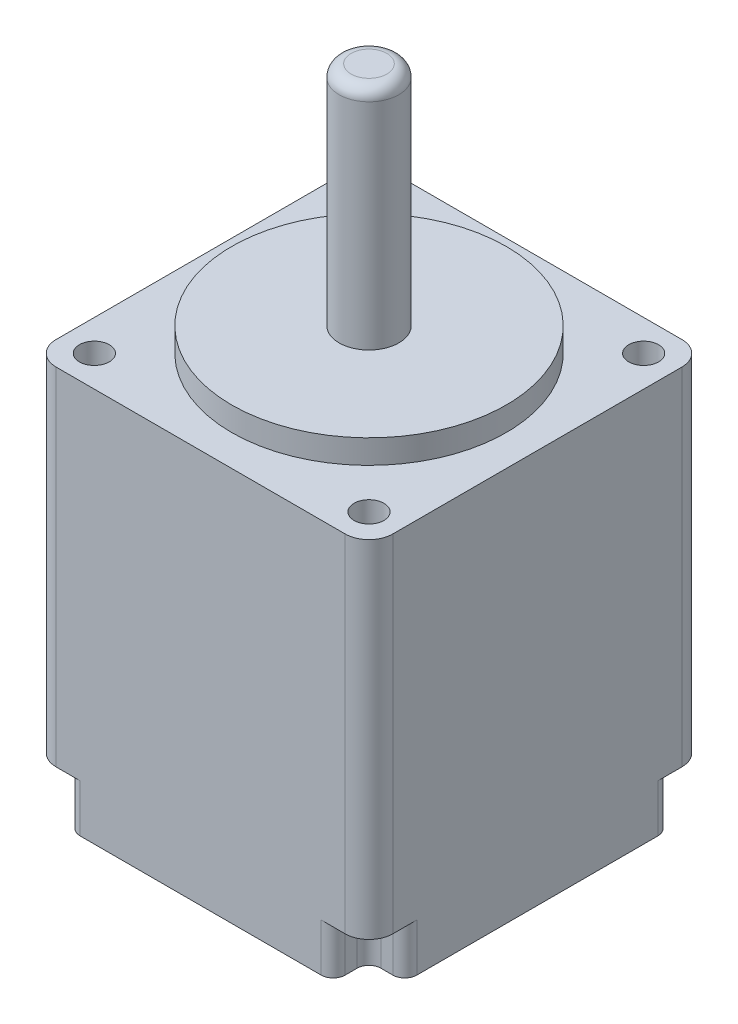
SolidWorks part; units mm, degrees
ref_plane "Front Plane" through (0, 0, 0) normal (0, 0, 1) x (1, 0, 0)
ref_plane "Top Plane" through (0, 0, 0) normal (0, 1, 0) x (1, 0, 0)
ref_plane "Right Plane" through (0, 0, 0) normal (1, 0, 0) x (0, 0, -1)
sketch "Sketch1" plane through (0, 0, 0) normal (0, 1, 0) x (1, 0, 0)
  line L1 (-14.1, 14.1) -> (14.1, 14.1)
  line L2 (-14.1, 14.1) -> (-14.1, -14.1)
  line L3 (-14.1, -14.1) -> (14.1, -14.1)
  line L4 (14.1, 14.1) -> (14.1, -14.1)
  line L5 (-14.1, 14.1) -> (14.1, -14.1) construction
  line L6 (-14.1, -14.1) -> (14.1, 14.1) construction
  point P0 (0, 0)
  dimension "D1" = 28.2
extrude "Boss-Extrude1" add sketch "Sketch1" along normal blind 33
sketch "Sketch2" plane through (0, 33, 0) normal (0, 1, 0) x (1, 0, 0)
  circle A0 centre (0, 0) radius 11.5
  dimension "D1" = 23
extrude "Boss-Extrude2" add sketch "Sketch2" along normal blind 2
sketch "Sketch3" plane through (0, 35, 0) normal (0, 1, 0) x (1, 0, 0)
  circle A0 centre (0, 0) radius 2.5
  dimension "D1" = 5
extrude "Boss-Extrude3" add sketch "Sketch3" along normal blind 19
sketch "Sketch4" plane through (0, 33, 0) normal (0, 1, 0) x (1, 0, 0)
  line L0 (14.1, 14.1) -> (-14.1, 14.1) construction
  line L1 (-14.1, 14.1) -> (-14.1, -14.1) construction
  circle A0 centre (-11.5, 11.5) radius 1.25
  dimension "D1" = 2.5
  dimension "D2" = 2.6
  dimension "D3" = 2.6
extrude "Cut-Extrude1" cut sketch "Sketch4" against normal blind 8
mirror "Mirror1" about plane through (0, 0, 0) normal (1, 0, 0) of "Cut-Extrude1"
mirror "Mirror2" about plane through (0, 0, 0) normal (0, 0, 1) of "Mirror1", "Cut-Extrude1"
sketch "Sketch5" plane through (0, 0, 0) normal (0, -1, 0) x (1, 0, 0)
  line L0 (-14.1, 14.1) -> (-11.1, 14.1)
  line L1 (-14.1, 14.1) -> (14.1, 14.1) construction
  line L2 (-11.1, 14.1) -> (-11.1, 11.1)
  line L3 (-11.1, 11.1) -> (-14.1, 11.1)
  line L5 (-14.1, 11.1) -> (-14.1, 14.1)
  dimension "D1" = 3
  dimension "D2" = 3
  dimension "D3" = 3
extrude "Cut-Extrude2" cut sketch "Sketch5" against normal blind 4
mirror "Mirror3" about plane through (0, 0, 0) normal (1, 0, 0) of "Cut-Extrude2"
mirror "Mirror4" about plane through (0, 0, 0) normal (0, 0, 1) of "Mirror3", "Cut-Extrude2"
sketch "Sketch6" plane through (0, 0, 0) normal (0, -1, 0) x (1, 0, 0)
  circle A0 centre (0, 0) radius 2.5
  dimension "D1" = 5
extrude "Cut-Extrude3" cut sketch "Sketch6" against normal blind 4
fillet "Fillet1" radius 2 4 edges at (-14.1, 18.5, -14.1) (14.1, 18.5, -14.1) (14.1, 18.5, 14.1) (-14.1, 18.5, 14.1)
fillet "Fillet2" radius 1 12 edges at (-14.1, 2, 11.1) (-11.1, 2, 14.1) (-11.1, 2, 11.1) (11.1, 2, 14.1) (11.1, 2, 11.1) (14.1, 2, 11.1) (14.1, 2, -11.1) (11.1, 2, -11.1) (11.1, 2, -14.1) (-14.1, 2, -11.1) (-11.1, 2, -11.1) (-11.1, 2, -14.1)
fillet "Fillet3" radius 1 1 edges at (0, 54, 2.5)
